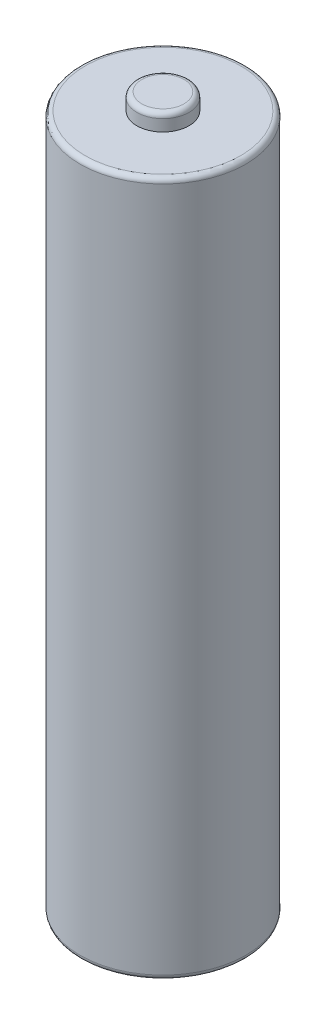
SolidWorks part; units mm, degrees
other "Camera1"
ref_plane "Front Plane" through (0, 0, 0) normal (0, 0, 1) x (1, 0, 0)
ref_plane "Top Plane" through (0, 0, 0) normal (0, 1, 0) x (1, 0, 0)
ref_plane "Right Plane" through (0, 0, 0) normal (1, 0, 0) x (0, 0, -1)
sketch "Sketch1" plane through (0, 0, 0) normal (0, 1, 0) x (1, 0, 0)
  circle A0 centre (0, 0) radius 5
extrude "Boss-Extrude1" add sketch "Sketch1" along normal blind 42
sketch "Sketch2" plane through (0, 42, 0) normal (0, 1, 0) x (1, 0, 0)
  circle A0 centre (0, 0) radius 1.575
  dimension "D1" = 3.15
extrude "Boss-Extrude2" add sketch "Sketch2" along normal blind 1
fillet "Fillet1" radius 0.3 3 edges at (0, 0, 5) (0, 42, 5) (0, 43, 1.575)
